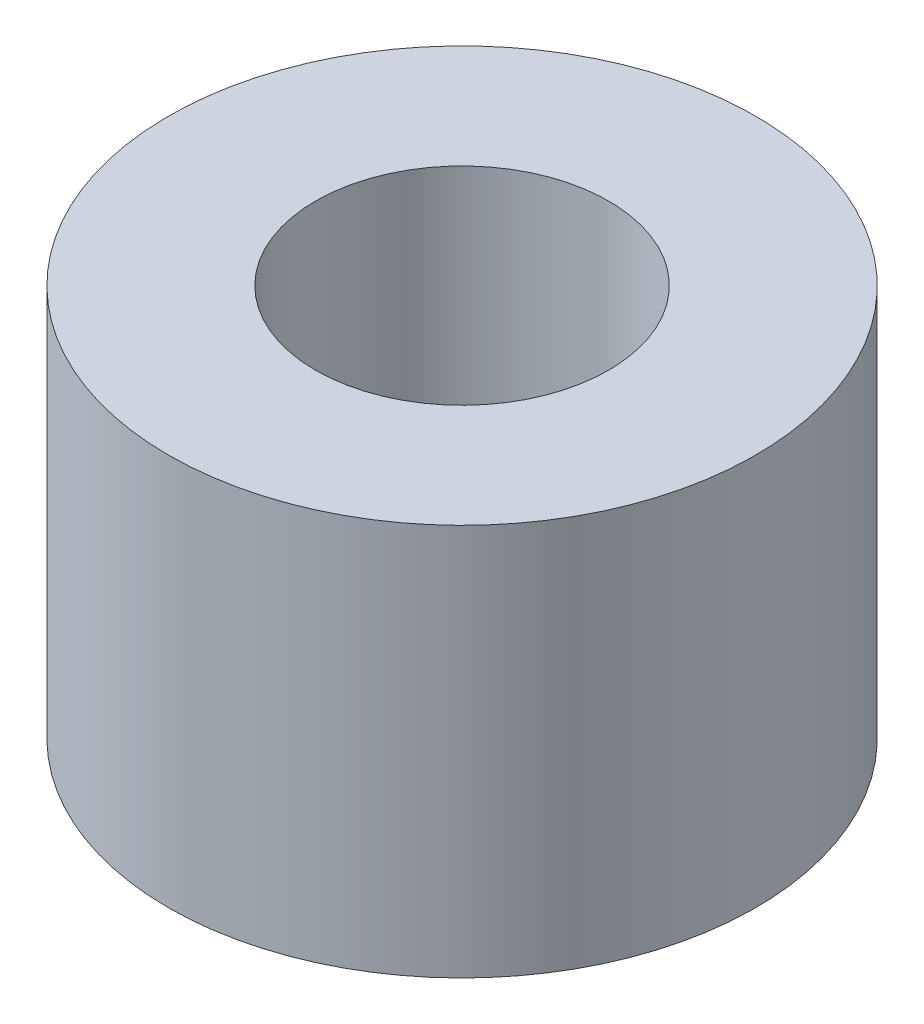
SolidWorks part; units mm, degrees
ref_plane "Alzado" through (0, 0, 0) normal (0, 0, 1) x (1, 0, 0)
ref_plane "Planta" through (0, 0, 0) normal (0, 1, 0) x (1, 0, 0)
ref_plane "Vista lateral" through (0, 0, 0) normal (1, 0, 0) x (0, 0, -1)
sketch "Croquis1" plane through (0, 0, 0) normal (0, 1, 0) x (1, 0, 0)
  circle A0 centre (0, 0.1239) radius 1.4956
  circle A1 centre (0, 0.1239) radius 2.9956
extrude "Saliente-Extruir1" add sketch "Croquis1" along normal blind 4
